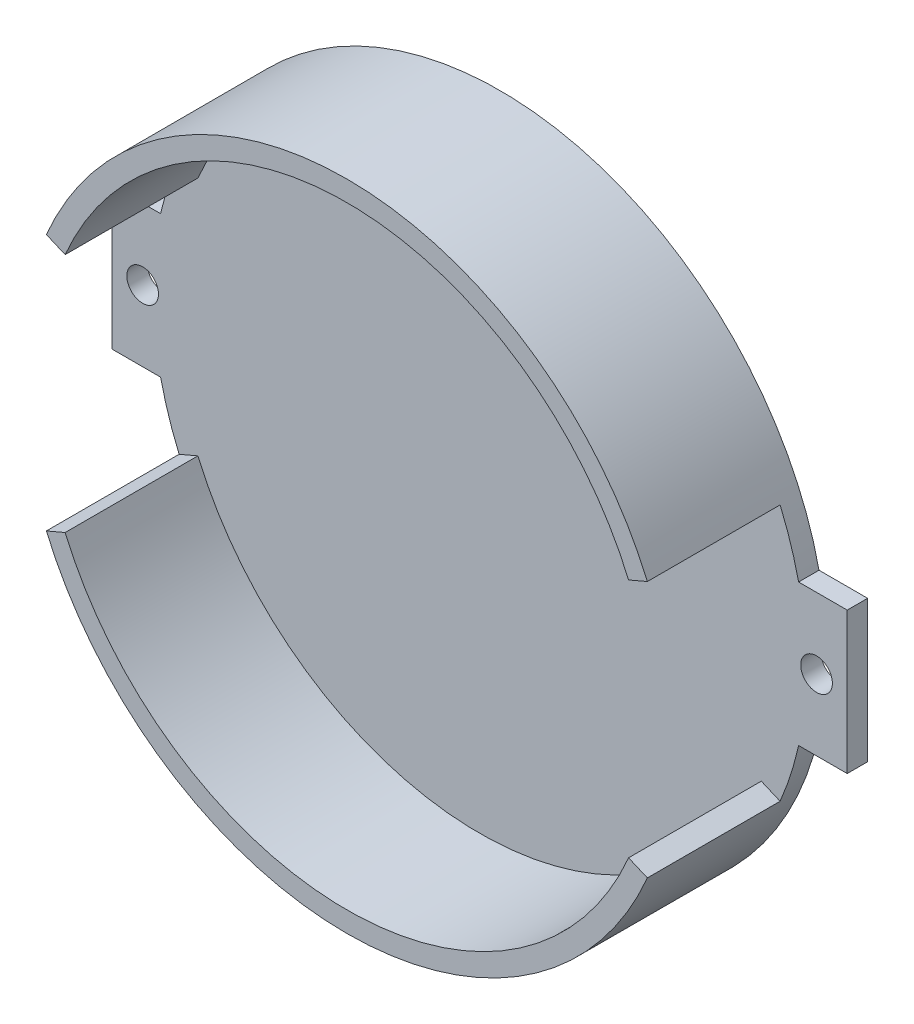
SolidWorks part; units mm, degrees
material "PVC 0.007 Plasticized"
ref_plane "Front Plane" through (0, 0, 0) normal (0, 0, 1) x (1, 0, 0)
ref_plane "Top Plane" through (0, 0, 0) normal (0, 1, 0) x (1, 0, 0)
ref_plane "Right Plane" through (0, 0, 0) normal (1, 0, 0) x (0, 0, -1)
sketch "Sketch1" plane through (0, 0, 0) normal (0, 0, 1) x (1, 0, 0)
  line L0 (-45.5449, 0) -> (46.7291, 0) construction
  line L2 (-31.2399, -6.9333) -> (-36, -6.9333)
  line L3 (-36, -6.9333) -> (-36, 6.9333)
  line L4 (-36, 6.9333) -> (-31.2399, 6.9333)
  line L5 (0, 32.8419) -> (0, -37.9086) construction
  line L6 (36, -6.9333) -> (36, 6.9333)
  line L7 (31.2399, -6.9333) -> (36, -6.9333)
  line L9 (36, 6.9333) -> (31.2399, 6.9333)
  arc A0 (-31.2399, -6.9333) -> (31.2399, -6.9333) centre (0, 0) ccw
  arc A1 (31.2399, 6.9333) -> (-31.2399, 6.9333) centre (0, 0) ccw
  point P8 (-32, 0)
  dimension "D1" = 72
  dimension "D2" = 32
extrude "Boss-Extrude1" add sketch "Sketch1" along normal blind 2
sketch "Sketch2" plane through (0, 0, 2) normal (0, 0, 1) x (1, 0, 0)
  line L0 (-29.4286, 12.5682) -> (-27.5893, 11.7827)
  line L1 (27.5893, -11.7827) -> (29.4286, -12.5682)
  line L2 (0, 35.0881) -> (0, -0.7639) construction
  line L3 (29.4286, 12.5682) -> (27.5893, 11.7827)
  line L4 (-27.5893, -11.7827) -> (-29.4286, -12.5682)
  arc A0 (-27.5893, -11.7827) -> (27.5893, -11.7827) centre (0, 0) ccw
  arc A1 (31.2399, 6.9333) -> (-31.2399, 6.9333) centre (0, 0) ccw construction
  arc A2 (29.4286, 12.5682) -> (-29.4286, 12.5682) centre (0, 0) ccw
  arc A3 (-31.2399, -6.9333) -> (31.2399, -6.9333) centre (0, 0) ccw construction
  arc A4 (-29.4286, -12.5682) -> (29.4286, -12.5682) centre (0, 0) ccw
  arc A5 (27.5893, 11.7827) -> (-27.5893, 11.7827) centre (0, 0) ccw
  dimension "D1" = 2
extrude "Boss-Extrude2" add sketch "Sketch2" along normal blind 13
sketch "Sketch3" plane through (0, 0, 0) normal (0, 0, -1) x (-1, 0, 0)
  line L1 (-36, -6.9333) -> (-36, 6.9333) construction
  line L3 (36, 6.9333) -> (36, -6.9333) construction
  circle A0 centre (-33, 0) radius 1.55
  circle A1 centre (33, 0) radius 1.55
  point P4 (0, 0)
  point P8 (0, 0)
  point P11 (-36, 0)
  point P12 (0, 0)
  point P13 (0, 0)
  dimension "D1" = 3.1
  dimension "D2" = 3
  dimension "D3" = 3
extrude "Cut-Extrude1" cut sketch "Sketch3" against normal through all
